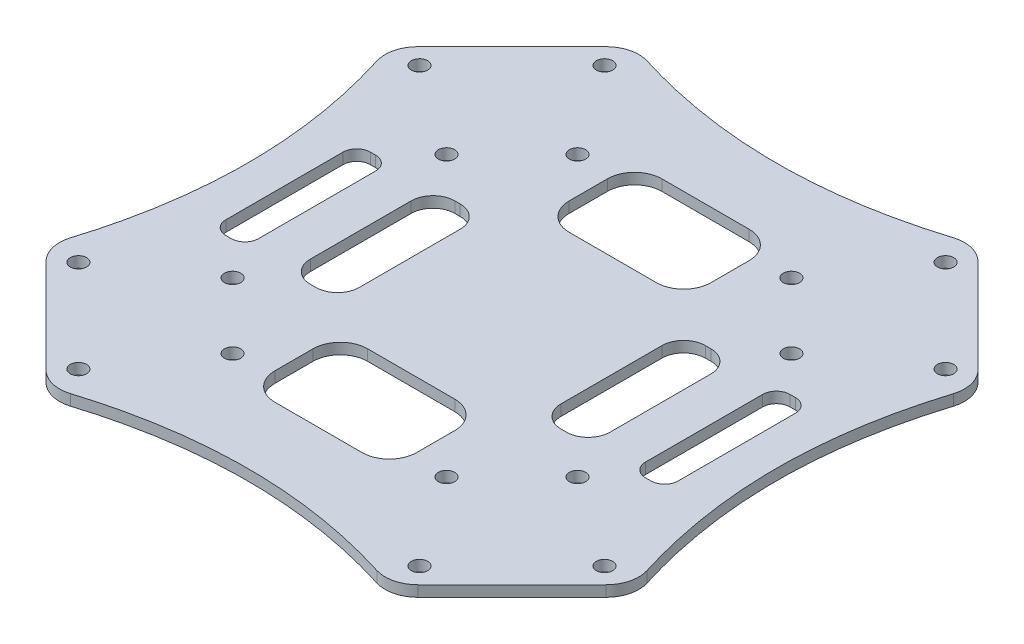
SolidWorks part; units mm, degrees
ref_plane "Спереди" through (0, 0, 0) normal (0, 0, 1) x (1, 0, 0)
ref_plane "Сверху" through (0, 0, 0) normal (0, 1, 0) x (1, 0, 0)
ref_plane "Справа" through (0, 0, 0) normal (1, 0, 0) x (0, 0, -1)
sketch "Эскиз2" plane through (0, 0, 0) normal (0, 1, 0) x (1, 0, 0)
  line L0 (-54, 0) -> (54, 0) construction
  line L1 (0, 54) -> (0, -54) construction
  line L2 (0, -48.5) -> (0, -35.5) construction
  line L3 (0, -35.5) -> (8, -35.5)
  line L4 (0, -35.5) -> (-8, -35.5)
  line L5 (-13, -30.5) -> (-13, -23.5)
  line L6 (-8, -18.5) -> (8, -18.5)
  line L7 (13, -23.5) -> (13, -30.5)
  line L8 (13, 23.5) -> (13, 30.5)
  line L9 (54, -31.5) -> (31.5, -54)
  line L10 (-8, 18.5) -> (8, 18.5)
  line L11 (-13, 30.5) -> (-13, 23.5)
  line L12 (-54, -31.5) -> (-31.5, -54)
  line L13 (54, 31.5) -> (31.5, 54)
  line L14 (0, 35.5) -> (-8, 35.5)
  line L15 (-54, 31.5) -> (-31.5, 54)
  line L16 (0, -48.5) -> (0, 48.5) construction
  line L17 (-48.5, 0) -> (48.5, 0) construction
  line L18 (0, 35.5) -> (8, 35.5)
  line L19 (-48.5, 0) -> (-41.5, 0)
  line L20 (-41.5, 0) -> (-41.5, 10.5)
  line L21 (-41.5, 0) -> (-41.5, -11.0066)
  line L22 (-39, -13.5066) -> (-38, -13.5066)
  line L23 (-35.5, -11.0066) -> (-35.5, 10.5)
  line L24 (-38, 13) -> (-39, 13)
  line L25 (-41.5, 0) -> (-35.5, 0)
  line L26 (-35.5, 0) -> (-27.5, 0)
  line L27 (-27.5, 0) -> (-27.5, 9)
  line L28 (-23.5, 13) -> (-22.5, 13)
  line L29 (-18.5, 9) -> (-18.5, -9.5066)
  line L30 (-22.5, -13.5066) -> (-23.5, -13.5066)
  line L31 (-27.5, -9.5066) -> (-27.5, 0)
  line L32 (27.5, -9.5066) -> (27.5, 0)
  line L33 (22.5, -13.5066) -> (23.5, -13.5066)
  line L34 (18.5, 9) -> (18.5, -9.5066)
  line L35 (23.5, 13) -> (22.5, 13)
  line L36 (27.5, 0) -> (27.5, 9)
  line L37 (35.5, 0) -> (27.5, 0)
  line L38 (41.5, 0) -> (35.5, 0)
  line L39 (38, 13) -> (39, 13)
  line L40 (35.5, -11.0066) -> (35.5, 10.5)
  line L41 (39, -13.5066) -> (38, -13.5066)
  line L42 (41.5, 0) -> (41.5, -11.0066)
  line L43 (41.5, 0) -> (41.5, 10.5)
  arc A0 (-13, -23.5) -> (-8, -18.5) centre (-8, -23.5) cw
  arc A1 (-8, -35.5) -> (-13, -30.5) centre (-8, -30.5) cw
  arc A2 (13, -30.5) -> (8, -35.5) centre (8, -30.5) cw
  arc A3 (8, -18.5) -> (13, -23.5) centre (8, -23.5) cw
  arc A4 (8, 18.5) -> (13, 23.5) centre (8, 23.5) ccw
  arc A5 (13, 30.5) -> (8, 35.5) centre (8, 30.5) ccw
  arc A6 (-8, 35.5) -> (-13, 30.5) centre (-8, 30.5) ccw
  arc A7 (-13, 23.5) -> (-8, 18.5) centre (-8, 23.5) ccw
  arc A8 (-38, -13.5066) -> (-35.5, -11.0066) centre (-38, -11.0066) ccw
  arc A9 (-41.5, -11.0066) -> (-39, -13.5066) centre (-39, -11.0066) ccw
  arc A10 (-41.5, 10.5) -> (-39, 13) centre (-39, 10.5) cw
  arc A11 (-35.5, 10.5) -> (-38, 13) centre (-38, 10.5) ccw
  arc A12 (-18.5, -9.5066) -> (-22.5, -13.5066) centre (-22.5, -9.5066) cw
  arc A13 (-23.5, -13.5066) -> (-27.5, -9.5066) centre (-23.5, -9.5066) cw
  arc A14 (-27.5, 9) -> (-23.5, 13) centre (-23.5, 9) cw
  arc A15 (-22.5, 13) -> (-18.5, 9) centre (-22.5, 9) cw
  arc A16 (22.5, 13) -> (18.5, 9) centre (22.5, 9) ccw
  arc A17 (27.5, 9) -> (23.5, 13) centre (23.5, 9) ccw
  arc A18 (23.5, -13.5066) -> (27.5, -9.5066) centre (23.5, -9.5066) ccw
  arc A19 (18.5, -9.5066) -> (22.5, -13.5066) centre (22.5, -9.5066) ccw
  arc A20 (35.5, 10.5) -> (38, 13) centre (38, 10.5) cw
  arc A21 (41.5, 10.5) -> (39, 13) centre (39, 10.5) ccw
  arc A22 (41.5, -11.0066) -> (39, -13.5066) centre (39, -11.0066) cw
  arc A23 (38, -13.5066) -> (35.5, -11.0066) centre (38, -11.0066) cw
  spline S0 degree 2 poles (31.5, 54) (0, 43) (-31.5, 54) knots 0 0 0 1 1 1
  spline S1 degree 2 poles (31.5, -54) (0, -43) (-31.5, -54) knots 0 0 0 1 1 1
  spline S2 degree 2 poles (-54, 31.5) (-43, 0) (-54, -31.5) knots 0 0 0 1 1 1
  spline S3 degree 2 poles (54, 31.5) (43, 0) (54, -31.5) knots 0 0 0 1 1 1
  point P23 (0, 0)
  dimension "D13" = 5
  dimension "D14" = 2.5
  dimension "D15" = 4
  dimension "D1" = 63
  dimension "D2" = 63
  dimension "D3" = 63
  dimension "D4" = 63
  dimension "D5" = 108
  dimension "D6" = 108
  dimension "D7" = 31.8198
  dimension "D8" = 31.8198
  dimension "D9" = 31.8198
  dimension "D10" = 31.8198
  dimension "D11" = 97
  dimension "D12" = 97
extrude "Бобышка-Вытянуть1" add sketch "Эскиз2" along normal blind 2
fillet "Скругление1" radius 6 8 edges at (-31.5, 1, 54) (-54, 1, 31.5) (-54, 1, -31.5) (-31.5, 1, -54) (31.5, 1, -54) (54, 1, -31.5) (54, 1, 31.5) (31.5, 1, 54)
sketch "Эскиз3" plane through (0, 0, 0) normal (0, -1, 0) x (1, 0, 0)
  line L0 (0, -48.5) -> (0, 48.5) construction
  line L1 (-48.5, 0) -> (48.5, 0) construction
  line L3 (42.75, -42.75) -> (-42.75, 42.75) construction
  line L5 (51.3866, -34.1134) -> (34.1134, -51.3866) construction
  line L7 (-51.3866, 34.1134) -> (-34.1134, 51.3866) construction
  line L8 (42.75, 42.75) -> (-42.75, -42.75) construction
  line L9 (51.3866, 34.1134) -> (34.1134, 51.3866) construction
  line L10 (-51.3866, -34.1134) -> (-34.1134, -51.3866) construction
  line L11 (-39.7748, 39.7748) -> (-48.26, 31.2895) construction
  line L12 (-25.6326, 25.6326) -> (-31.643, 19.6222) construction
  line L13 (-25.6326, 25.6326) -> (-19.6222, 31.643) construction
  line L14 (-39.7748, 39.7748) -> (-31.2895, 48.26) construction
  circle A0 centre (-19.6222, 31.643) radius 1.5
  circle A1 centre (-31.643, 19.6222) radius 1.5
  circle A2 centre (-48.26, 31.2895) radius 1.5
  circle A3 centre (-31.2895, 48.26) radius 1.5
  circle A4 centre (19.6222, 31.643) radius 1.5
  circle A5 centre (31.643, 19.6222) radius 1.5
  circle A6 centre (48.26, 31.2895) radius 1.5
  circle A7 centre (31.2895, 48.26) radius 1.5
  circle A8 centre (31.643, -19.6222) radius 1.5
  circle A9 centre (48.26, -31.2895) radius 1.5
  circle A10 centre (31.2895, -48.26) radius 1.5
  circle A11 centre (19.6222, -31.643) radius 1.5
  circle A12 centre (-19.6222, -31.643) radius 1.5
  circle A13 centre (-31.643, -19.6222) radius 1.5
  circle A14 centre (-48.26, -31.2895) radius 1.5
  circle A15 centre (-31.2895, -48.26) radius 1.5
  parabola Q1 (28.087, -52.8727) -> (-28.087, -52.8727) focus (0, -93.6023) apex (0, -48.5) construction
  parabola Q2 (28.087, 52.8727) -> (-28.087, 52.8727) focus (0, 93.6023) apex (0, 48.5) construction
  parabola Q3 (-52.8727, -28.087) -> (-52.8727, 28.087) focus (-93.6023, 0) apex (-48.5, 0) construction
  parabola Q4 (52.8727, -28.087) -> (52.8727, 28.087) focus (93.6023, 0) apex (48.5, 0) construction
  dimension "D1" = 120.9153
  dimension "D2" = 120.9153
  dimension "D5" = 36.25
  dimension "D6" = 24
  dimension "D3" = 97
  dimension "D4" = 97
  dimension "D7" = 20
  dimension "D8" = 12
  dimension "D9" = 12
  dimension "D10" = 8.5
  dimension "D11" = 8.5
extrude "Вырез-Вытянуть1" cut sketch "Эскиз3" against normal blind 10
